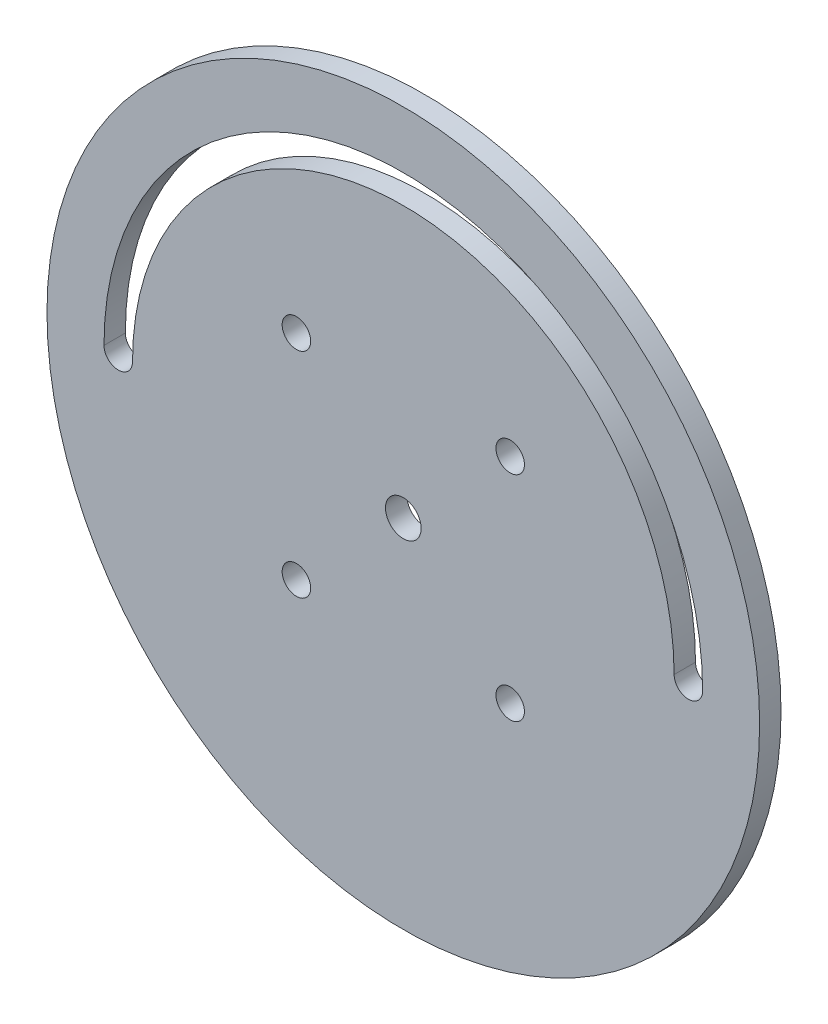
SolidWorks part; units mm, degrees
ref_plane "Front" through (0, 0, 0) normal (0, 0, 1) x (1, 0, 0)
ref_plane "Top" through (0, 0, 0) normal (0, 1, 0) x (1, 0, 0)
ref_plane "Right" through (0, 0, 0) normal (1, 0, 0) x (0, 0, -1)
sketch "Sketch1" plane through (0, 0, 0) normal (0, 0, 1) x (1, 0, 0)
  circle A0 centre (0, 0) radius 50
  arc A1 (-40, 0) -> (40, 0) centre (0, 0) cw construction
  arc A2 (42, 0) -> (-42, 0) centre (0, 0) ccw
  arc A3 (38, 0) -> (-38, 0) centre (0, 0) ccw
  arc A4 (38, 0) -> (42, 0) centre (40, 0) ccw
  arc A5 (-42, 0) -> (-38, 0) centre (-40, 0) ccw
  circle A6 centre (0, 0) radius 2.5
  point P5 (0, 40)
  dimension "D1" = 100
  dimension "D2" = 2
  dimension "D3" = 40
  dimension "D4" = 5
extrude "Boss-Extrude1" add sketch "Sketch1" along normal blind 3
sketch "Sketch2" plane through (0, 0, 3) normal (0, 0, 1) x (1, 0, 0)
  line L1 (-15, 15) -> (15, 15) construction
  line L2 (-15, 15) -> (-15, -15) construction
  line L3 (-15, -15) -> (15, -15) construction
  line L4 (15, 15) -> (15, -15) construction
  line L5 (-15, 15) -> (15, -15) construction
  line L6 (-15, -15) -> (15, 15) construction
  circle A4 centre (-15, 15) radius 2
  circle A5 centre (15, 15) radius 2
  circle A6 centre (15, -15) radius 2
  circle A7 centre (-15, -15) radius 2
  point P0 (0, 0)
  dimension "D2" = 4
  dimension "D1" = 30
extrude "Cut-Extrude1" cut sketch "Sketch2" against normal through all
equation "\"D3@Sketch1\"=\"D1@Sketch1\"/2-10"
